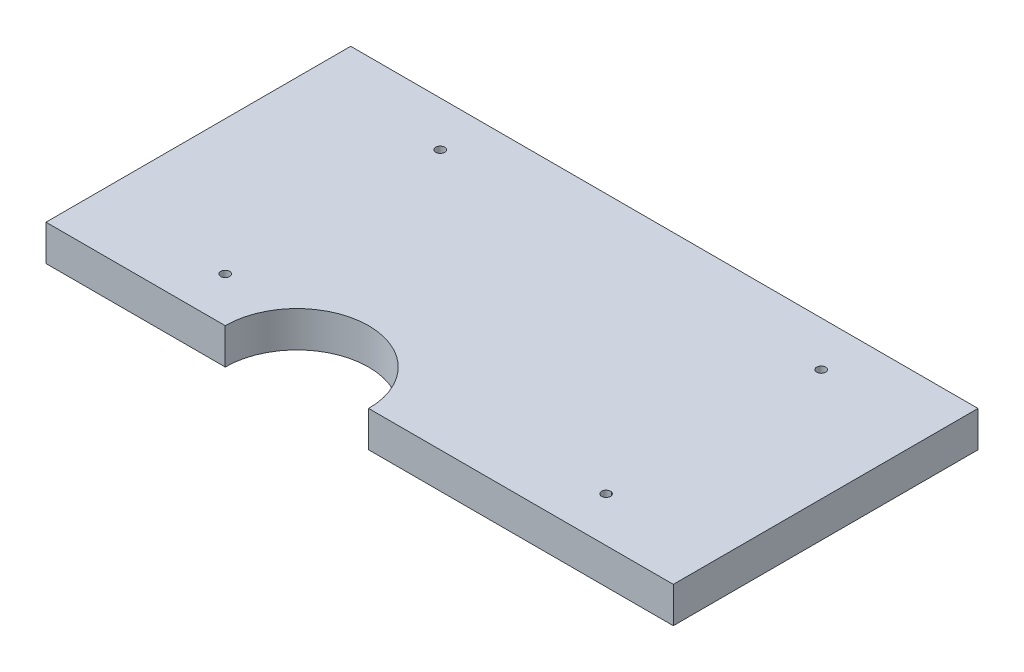
SolidWorks part; units mm, degrees
ref_plane "Front Plane" through (0, 0, 0) normal (0, 0, 1) x (1, 0, 0)
ref_plane "Top Plane" through (0, 0, 0) normal (0, 1, 0) x (1, 0, 0)
ref_plane "Right Plane" through (0, 0, 0) normal (1, 0, 0) x (0, 0, -1)
sketch "Sketch1" plane through (0, 0, 0) normal (0, 1, 0) x (1, 0, 0)
  line L0 (-32.6753, 32.7463) -> (-32.6753, -30.8949) construction
  line L1 (-62.6753, 42.7463) -> (77.3247, 42.7463)
  line L2 (-62.6753, 42.7463) -> (-62.6753, -25.2537)
  line L3 (9.3247, -25.2537) -> (77.3247, -25.2537)
  line L4 (77.3247, 42.7463) -> (77.3247, -25.2537)
  line L5 (52.3247, 57.5201) -> (52.3247, -27.5736) construction
  line L6 (-62.6753, -25.2537) -> (-22.6753, -25.2537)
  line L7 (-32.6753, -15.2537) -> (91.9519, -15.2537) construction
  line L8 (-32.6753, 32.7463) -> (97.4549, 32.7463) construction
  circle A0 centre (-32.6753, 32.7463) radius 1
  circle A1 centre (-32.6753, -15.2537) radius 1
  circle A2 centre (52.3247, 32.7463) radius 1
  circle A3 centre (52.3247, -15.2537) radius 1
  arc A4 (9.3247, -25.2537) -> (-22.6753, -25.2537) centre (-6.6753, -25.2537) ccw
  dimension "D5" = 2
  dimension "D6" = 2
  dimension "D7" = 85
  dimension "D8" = 56
  dimension "D9" = 16
  dimension "D1" = 68
  dimension "D2" = 140
  dimension "D3" = 10
  dimension "D4" = 10
  dimension "D10" = 25
extrude "Boss-Extrude1" add sketch "Sketch1" along normal blind 8
